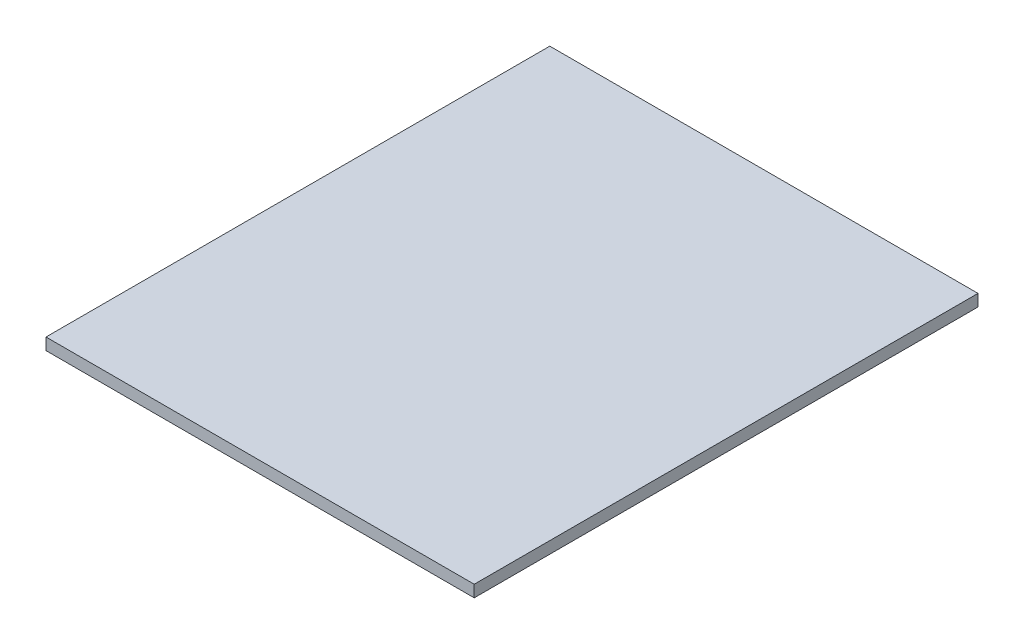
SolidWorks part; units mm, degrees
material "Pine"
ref_plane "Front Plane" through (0, 0, 0) normal (0, 0, 1) x (1, 0, 0)
ref_plane "Top Plane" through (0, 0, 0) normal (0, 1, 0) x (1, 0, 0)
ref_plane "Right Plane" through (0, 0, 0) normal (1, 0, 0) x (0, 0, -1)
sketch "Sketch1" plane through (0, 0, 0) normal (0, 1, 0) x (1, 0, 0)
  line L1 (-215.9, -254) -> (215.9, -254)
  line L2 (-215.9, -254) -> (-215.9, 254)
  line L3 (-215.9, 254) -> (215.9, 254)
  line L4 (215.9, -254) -> (215.9, 254)
  line L5 (-215.9, -254) -> (215.9, 254) construction
  line L6 (-215.9, 254) -> (215.9, -254) construction
  point P0 (0, 0)
  dimension "D1" = 508
  dimension "D2" = 431.8
extrude "Boss-Extrude1" add sketch "Sketch1" along normal blind 11.9062
